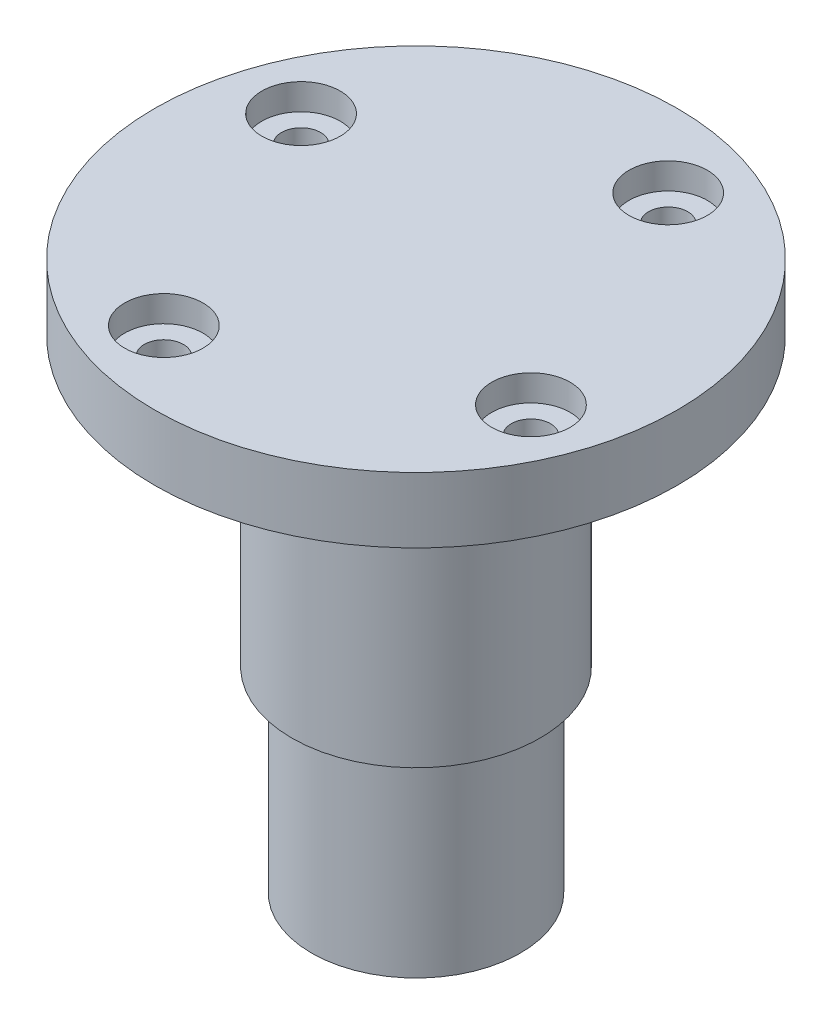
SolidWorks part; units mm, degrees
ref_plane "前视基准面" through (0, 0, 0) normal (0, 0, 1) x (1, 0, 0)
ref_plane "上视基准面" through (0, 0, 0) normal (0, 1, 0) x (1, 0, 0)
ref_plane "右视基准面" through (0, 0, 0) normal (1, 0, 0) x (0, 0, -1)
sketch "草图1" plane through (0, 0, 0) normal (0, 1, 0) x (1, 0, 0)
  circle A0 centre (0, 0) radius 8
  dimension "D1" = 16
extrude "凸台-拉伸1" add sketch "草图1" along normal blind 37
sketch "草图2" plane through (0, 37, 0) normal (0, 1, 0) x (1, 0, 0)
  circle A0 centre (0, 0) radius 9.5
  dimension "D1" = 19
extrude "凸台-拉伸2" add sketch "草图2" against normal blind 22
sketch "草图3" plane through (0, 37, 0) normal (0, 1, 0) x (1, 0, 0)
  circle A0 centre (0, 0) radius 10
  circle A1 centre (0, 0) radius 20
  dimension "D1" = 20
  dimension "D2" = 40
extrude "凸台-拉伸3" add sketch "草图3" along normal blind 5 contours A1
sketch "草图4" plane through (0, 42, 0) normal (0, 1, 0) x (1, 0, 0)
  line L0 (-5.2523, -14.0504) -> (0, 0) construction
  line L1 (-18.7338, 7.0031) -> (18.7338, -7.0031) construction
  line L2 (3.5016, 9.3669) -> (7.0031, 18.7338) construction
  line L3 (3.5016, 9.3669) -> (7.0031, 18.7338) construction
  line L4 (5.2523, 14.0504) -> (7.1939, 13.3246) construction
  circle A0 centre (0, 0) radius 10
  circle A1 centre (0, 0) radius 20 construction
  circle A2 centre (5.2523, 14.0504) radius 1.5
  circle A6 centre (14.0504, -5.2523) radius 1.5
  circle A7 centre (-5.2523, -14.0504) radius 1.5
  circle A8 centre (-14.0504, 5.2523) radius 1.5
  point P8 (0, 0)
  point P10 (0, 0)
  point P24 (-0.7332, 1.6086)
  point P25 (0, 0)
  dimension "D1" = 20
  dimension "D2" = 3
  dimension "D3" = 4
extrude "切除-拉伸1" cut sketch "草图4" against normal blind 5 contours A8 | A2 | A6 | A7
sketch "草图5" plane through (0, 42, 0) normal (0, 1, 0) x (1, 0, 0)
  circle A0 centre (-14.0504, 5.2523) radius 3
  circle A1 centre (5.2523, 14.0504) radius 3
  circle A2 centre (14.0504, -5.2523) radius 3
  circle A3 centre (-5.2523, -14.0504) radius 3
  point P12 (0, 0)
  dimension "D1" = 6
  dimension "D2" = 4
extrude "切除-拉伸2" cut sketch "草图5" against normal blind 2
